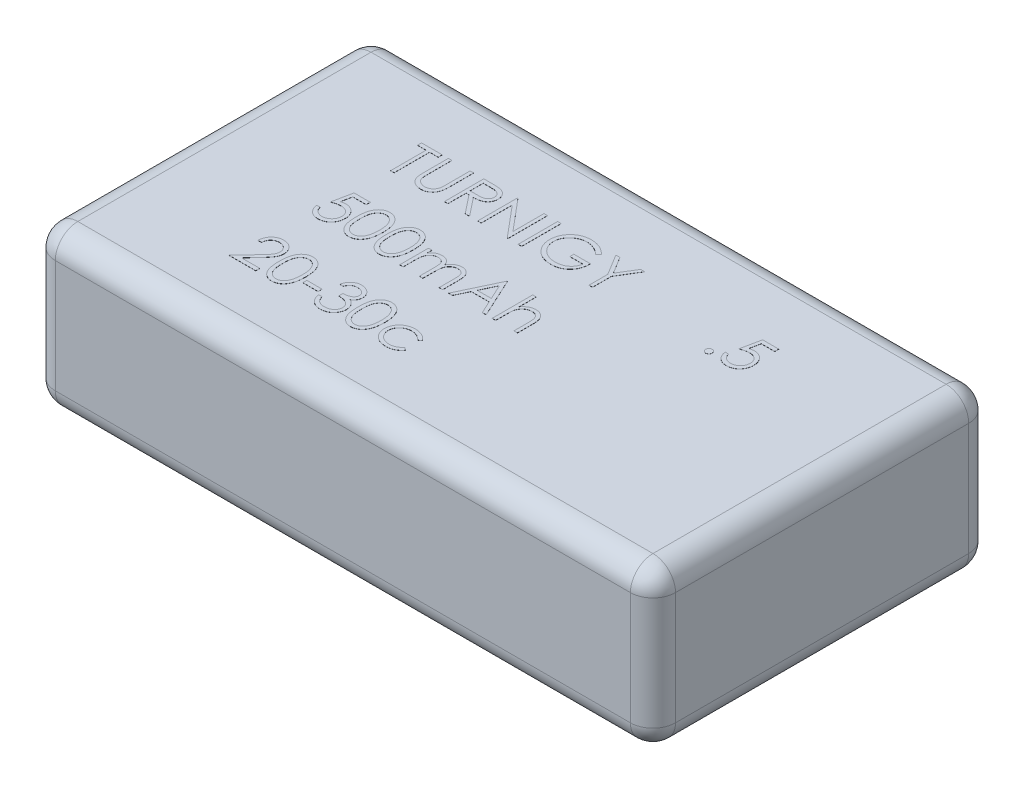
SolidWorks part; units mm, degrees
ref_plane "Front Plane" through (0, 0, 0) normal (0, 0, 1) x (1, 0, 0)
ref_plane "Top Plane" through (0, 0, 0) normal (0, 1, 0) x (1, 0, 0)
ref_plane "Right Plane" through (0, 0, 0) normal (1, 0, 0) x (0, 0, -1)
sketch "Sketch1" plane through (0, 0, 0) normal (0, 1, 0) x (1, 0, 0)
  line L1 (-27.5, 15) -> (27.5, 15)
  line L2 (-27.5, 15) -> (-27.5, -15)
  line L3 (-27.5, -15) -> (27.5, -15)
  line L4 (27.5, 15) -> (27.5, -15)
  line L5 (-27.5, 15) -> (27.5, -15) construction
  line L6 (-27.5, -15) -> (27.5, 15) construction
  point P0 (0, 0)
  dimension "D1" = 55
  dimension "D2" = 30
extrude "Boss-Extrude1" add sketch "Sketch1" along normal blind 14
fillet "Fillet1" radius 2 12 edges at (-27.5, 7, 15) (27.5, 7, 15) (27.5, 7, -15) (-27.5, 7, -15) (0, 0, 15) (-27.5, 0, 0) (27.5, 0, 0) (0, 0, -15) (-27.5, 14, 0) (0, 14, 15) (27.5, 14, 0) (0, 14, -15)
sketch "Sketch4" plane through (0, 14, 0) normal (0, 1, 0) x (1, 0, 0)
  text T0 "TURNIGY      .5\r\n500mAh\r\n20-30c\r\n"
extrude "Boss-Extrude2" add sketch "Sketch4" along normal blind 0.01
sketch "Sketch5" plane through (0, 14, 0) normal (0, 1, 0) x (1, 0, 0)
  line L0 (0, -13) -> (0, 13) construction
  line L1 (-25.5, -13) -> (25.5, -13) construction
  line L2 (25.5, 13) -> (-25.5, 13) construction
  line L3 (25.5, 0) -> (-25.5, 0) construction
  line L4 (25.5, -13) -> (25.5, 13) construction
  line L5 (-25.5, 13) -> (-25.5, -13) construction
